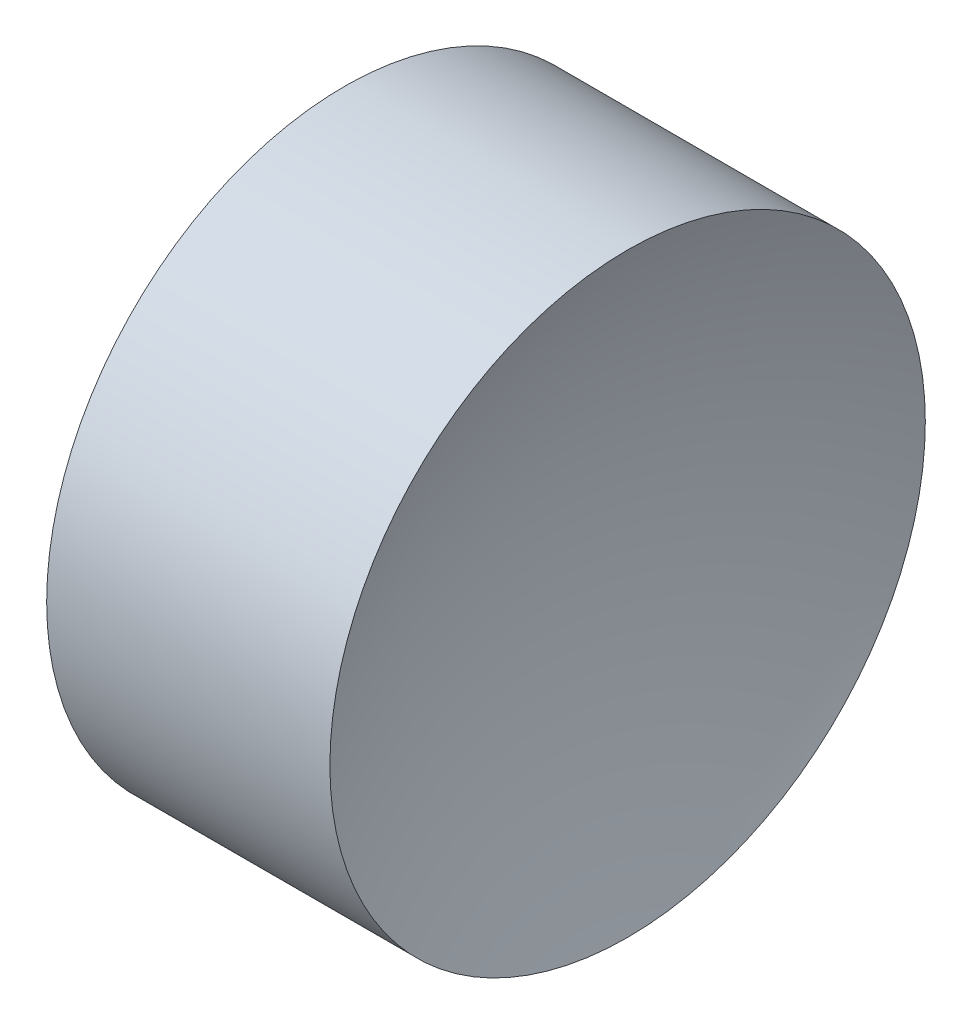
SolidWorks part; units mm, degrees
ref_plane "前视基准面" through (0, 0, 0) normal (0, 0, 1) x (1, 0, 0)
ref_plane "上视基准面" through (0, 0, 0) normal (0, 1, 0) x (1, 0, 0)
ref_plane "右视基准面" through (0, 0, 0) normal (1, 0, 0) x (0, 0, -1)
sketch "草图1" plane through (0, 0, 0) normal (0, 0, 1) x (1, 0, 0)
  line L0 (10.342, 6.5156) -> (13.4985, 6.5156) construction
  line L1 (11.157, 6.5156) -> (11.157, 8.5156)
  line L2 (12.657, 6.5156) -> (11.157, 6.5156)
  line L4 (11.157, 8.5156) -> (13.0595, 8.5156)
  arc A0 (13.0595, 8.5156) -> (12.657, 6.5156) centre (17.827, 6.5156) ccw
revolve "旋转1" add sketch "草图1" angle 360 about L0
